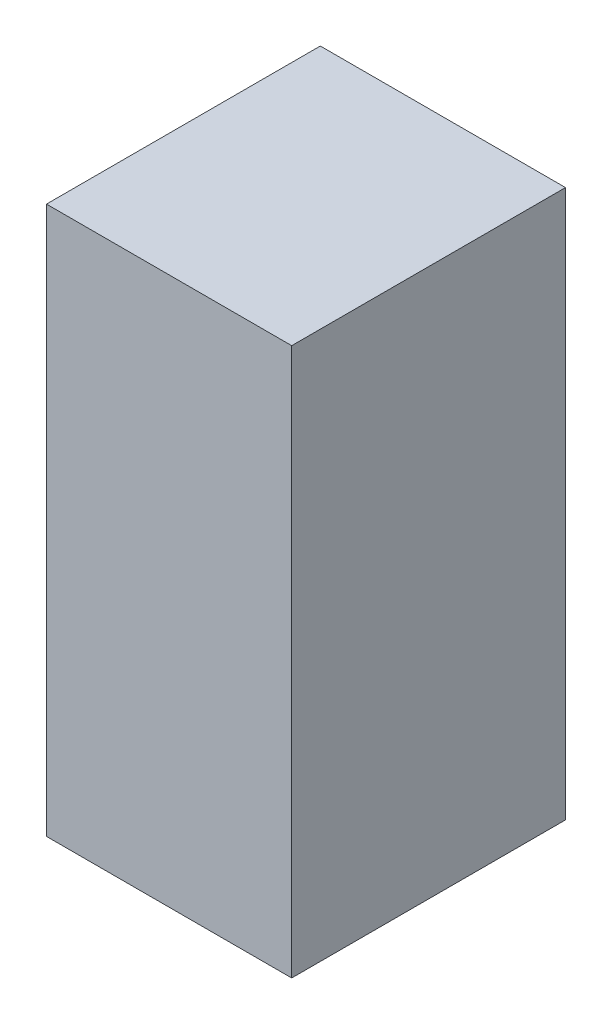
SolidWorks part; units mm, degrees
ref_plane "Front Plane" through (0, 0, 0) normal (0, 0, 1) x (1, 0, 0)
ref_plane "Top Plane" through (0, 0, 0) normal (0, 1, 0) x (1, 0, 0)
ref_plane "Right Plane" through (0, 0, 0) normal (1, 0, 0) x (0, 0, -1)
sketch "Sketch1" plane through (0, 0, 0) normal (0, 0, 1) x (1, 0, 0)
  line L0 (-30, 0) -> (30, 0)
  line L4 (30, 134) -> (-30, 134)
  line L5 (30, 134) -> (30, 0)
  line L7 (-30, 134) -> (-30, 0)
extrude "Extrude1" add sketch "Sketch1" along normal blind 67
